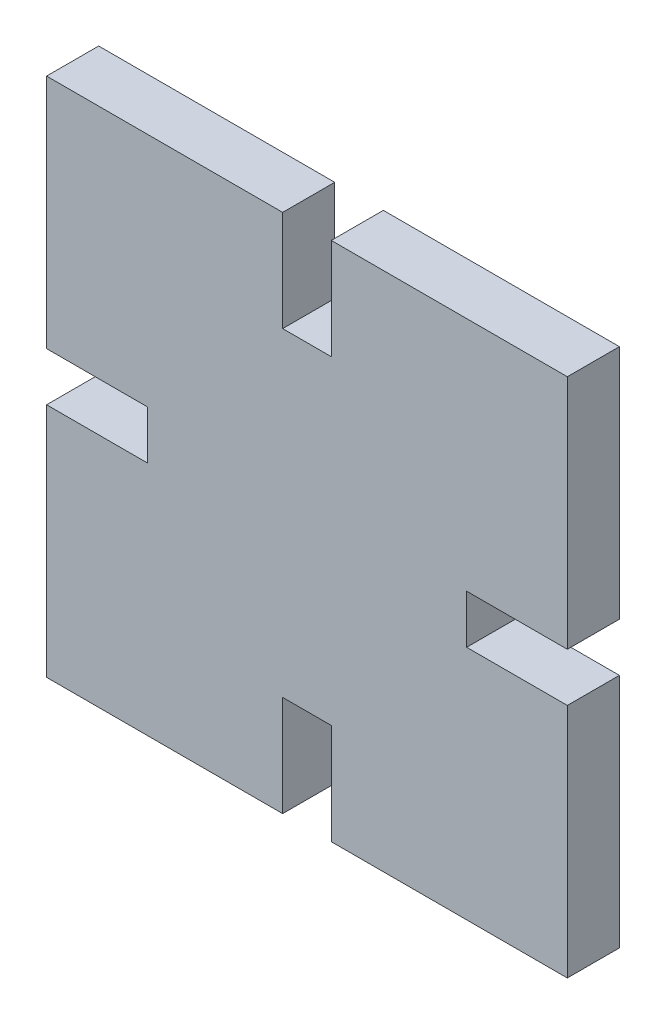
SolidWorks part; units mm, degrees
ref_plane "Front Plane" through (0, 0, 0) normal (0, 0, 1) x (1, 0, 0)
ref_plane "Top Plane" through (0, 0, 0) normal (0, 1, 0) x (1, 0, 0)
ref_plane "Right Plane" through (0, 0, 0) normal (1, 0, 0) x (0, 0, -1)
sketch "Sketch1" plane through (0, 0, 0) normal (0, 0, 1) x (1, 0, 0)
  line L1 (-15, -15) -> (15, -15)
  line L2 (-15, -15) -> (-15, 15)
  line L3 (-15, 15) -> (15, 15)
  line L4 (15, -15) -> (15, 15)
  line L5 (-15, -15) -> (15, 15) construction
  line L6 (-15, 15) -> (15, -15) construction
  point P0 (0, 0)
extrude "Boss-Extrude1" add sketch "Sketch1" along normal blind 3
sketch "Sketch2" plane through (0, 0, 3) normal (0, 0, 1) x (1, 0, 0)
  line L0 (-1.4, 9.2) -> (-1.4, 15)
  line L1 (-1.4, 9.2) -> (1.4, 9.2)
  line L2 (-1.4, 15) -> (1.4, 15)
  line L3 (1.4, 9.2) -> (1.4, 15)
  line L4 (-1.4, 9.2) -> (1.4, 15) construction
  line L5 (-1.4, 15) -> (1.4, 9.2) construction
  line L6 (-15, 0) -> (15, 0) construction
  line L7 (-15, 15) -> (-15, -15) construction
  line L8 (15, -15) -> (15, 15) construction
  line L9 (0, 15) -> (0, -15) construction
  line L10 (-15, -15) -> (15, -15) construction
  line L11 (15, 15) -> (-15, 15) construction
  line L12 (-1.4, -15) -> (1.4, -15)
  line L13 (-1.4, -9.2) -> (-1.4, -15)
  line L14 (1.4, -9.2) -> (1.4, -15)
  line L15 (-1.4, -9.2) -> (1.4, -9.2)
  line L16 (-9.2, -1.4) -> (-15, -1.4)
  line L17 (-9.2, -1.4) -> (-9.2, 1.4)
  line L18 (-15, -1.4) -> (-15, 1.4)
  line L19 (-9.2, 1.4) -> (-15, 1.4)
  line L20 (-9.2, -1.4) -> (-15, 1.4) construction
  line L21 (-15, -1.4) -> (-9.2, 1.4) construction
  line L22 (15, -1.4) -> (15, 1.4)
  line L23 (9.2, -1.4) -> (15, -1.4)
  line L24 (9.2, -1.4) -> (9.2, 1.4)
  line L25 (9.2, 1.4) -> (15, 1.4)
  point P1 (0, 12.1)
  point P15 (0, 0)
  point P24 (-12.1, 0)
extrude "Cut-Extrude1" cut sketch "Sketch2" against normal through all both and the other way through all
equation "\"material_width\"= 30"
equation "\"kerf\"= 0.1"
equation "\"material_thickness\"= 3"
equation "\"slot_width\"= \"material_thickness\" - \"kerf\" * 2"
equation "\"D1@Sketch1\"=\"material_width\""
equation "\"D1@Boss-Extrude1\"=\"material_thickness\""
equation "\"D1@Sketch2\"=\"slot_width\""
equation "\"D2@Sketch2\"=\"material_thickness\" +\"slot_width\""
